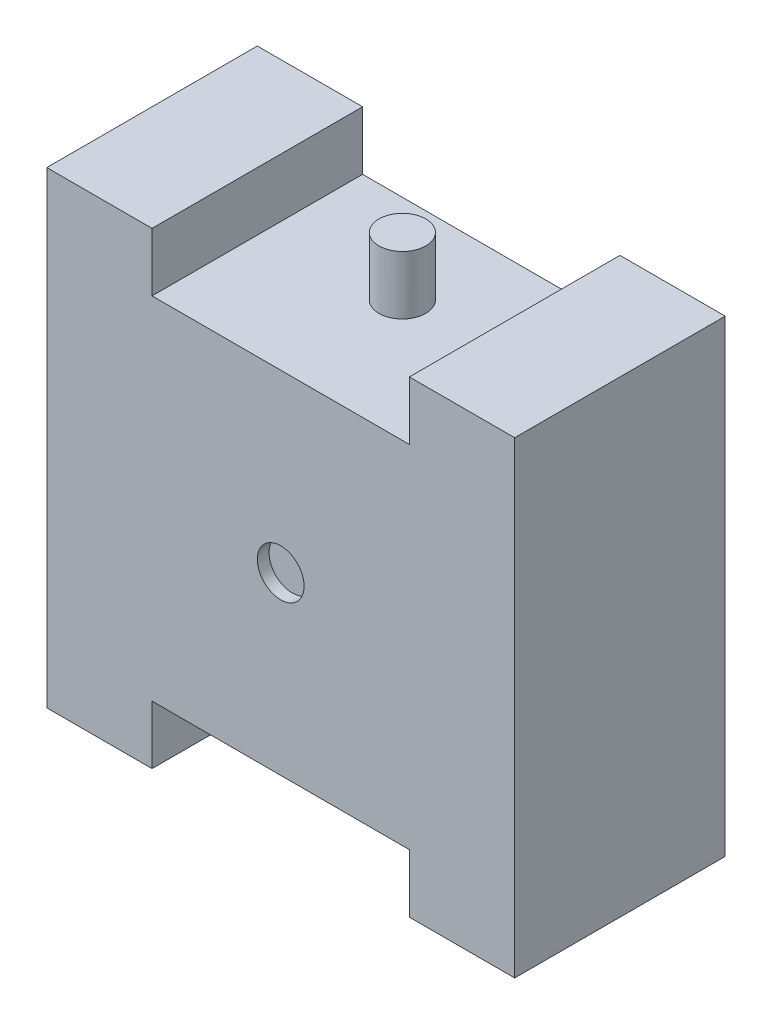
SolidWorks part; units mm, degrees
ref_plane "Front Plane" through (0, 0, 0) normal (0, 0, 1) x (1, 0, 0)
ref_plane "Top Plane" through (0, 0, 0) normal (0, 1, 0) x (1, 0, 0)
ref_plane "Right Plane" through (0, 0, 0) normal (1, 0, 0) x (0, 0, -1)
sketch "Sketch1" plane through (0, 0, 0) normal (0, 0, 1) x (1, 0, 0)
  line L0 (-275, 500) -> (-275, 375)
  line L1 (-500, -500) -> (-275, -500)
  line L2 (-500, -500) -> (-500, 500)
  line L3 (-500, 500) -> (-275, 500)
  line L4 (500, -500) -> (500, 500)
  line L5 (-500, -500) -> (500, 500) construction
  line L6 (-500, 500) -> (500, -500) construction
  line L7 (-275, 375) -> (275, 375)
  line L8 (275, 375) -> (275, 500)
  line L9 (-500, 0) -> (500, 0) construction
  line L10 (275, -375) -> (275, -500)
  line L11 (-275, -375) -> (275, -375)
  line L12 (-275, -500) -> (-275, -375)
  line L13 (275, 500) -> (500, 500)
  line L14 (275, -500) -> (500, -500)
  point P0 (0, 0)
  dimension "D1" = 1000
  dimension "D2" = 1000
  dimension "D3" = 125
  dimension "D4" = 550
  dimension "D5" = 225
extrude "Boss-Extrude1" add sketch "Sketch1" along normal blind 450
sketch "Sketch2" plane through (0, -375, 0) normal (0, -1, 0) x (1, 0, 0)
  line L0 (0, 0) -> (0, 450) construction
  line L1 (-275, 450) -> (275, 450) construction
  circle A0 centre (0, 190) radius 50
  dimension "D1" = 100
  dimension "D2" = 190
extrude "Boss-Extrude2" add sketch "Sketch2" along normal blind 125
sketch "Sketch3" plane through (0, 375, 0) normal (0, 1, 0) x (1, 0, 0)
  line L0 (0, 0) -> (0, -450) construction
  line L1 (275, 0) -> (-275, 0) construction
  line L2 (275, -450) -> (-275, -450) construction
  circle A0 centre (0, -190) radius 50
  dimension "D1" = 100
  dimension "D2" = 190
extrude "Boss-Extrude3" add sketch "Sketch3" along normal blind 125
sketch "Sketch4" plane through (0, 0, 450) normal (0, 0, 1) x (1, 0, 0)
  circle A0 centre (0, 0) radius 50
  dimension "D1" = 100
extrude "Cut-Extrude1" cut sketch "Sketch4" against normal blind 25
sketch "Sketch5" plane through (0, 0, 0) normal (0, 0, -1) x (-1, 0, 0)
  line L0 (0, 375) -> (0, -375) construction
  line L1 (300, -50) -> (400, -50)
  line L2 (300, -50) -> (300, 50)
  line L3 (300, 50) -> (400, 50)
  line L4 (400, -50) -> (400, 50)
  line L5 (300, -50) -> (400, 50) construction
  line L6 (300, 50) -> (400, -50) construction
  line L7 (-275, 375) -> (275, 375) construction
  line L8 (-50, -375) -> (50, -375) construction
  line L9 (-300, 50) -> (-400, -50) construction
  line L10 (-300, -50) -> (-400, 50) construction
  line L11 (-400, -50) -> (-400, 50)
  line L12 (-300, 50) -> (-400, 50)
  line L13 (-300, -50) -> (-300, 50)
  line L14 (-300, -50) -> (-400, -50)
  point P0 (350, 0)
  point P16 (-350, 0)
  dimension "D1" = 100
  dimension "D2" = 100
  dimension "D3" = 350
extrude "Cut-Extrude2" cut sketch "Sketch5" against normal blind 25
